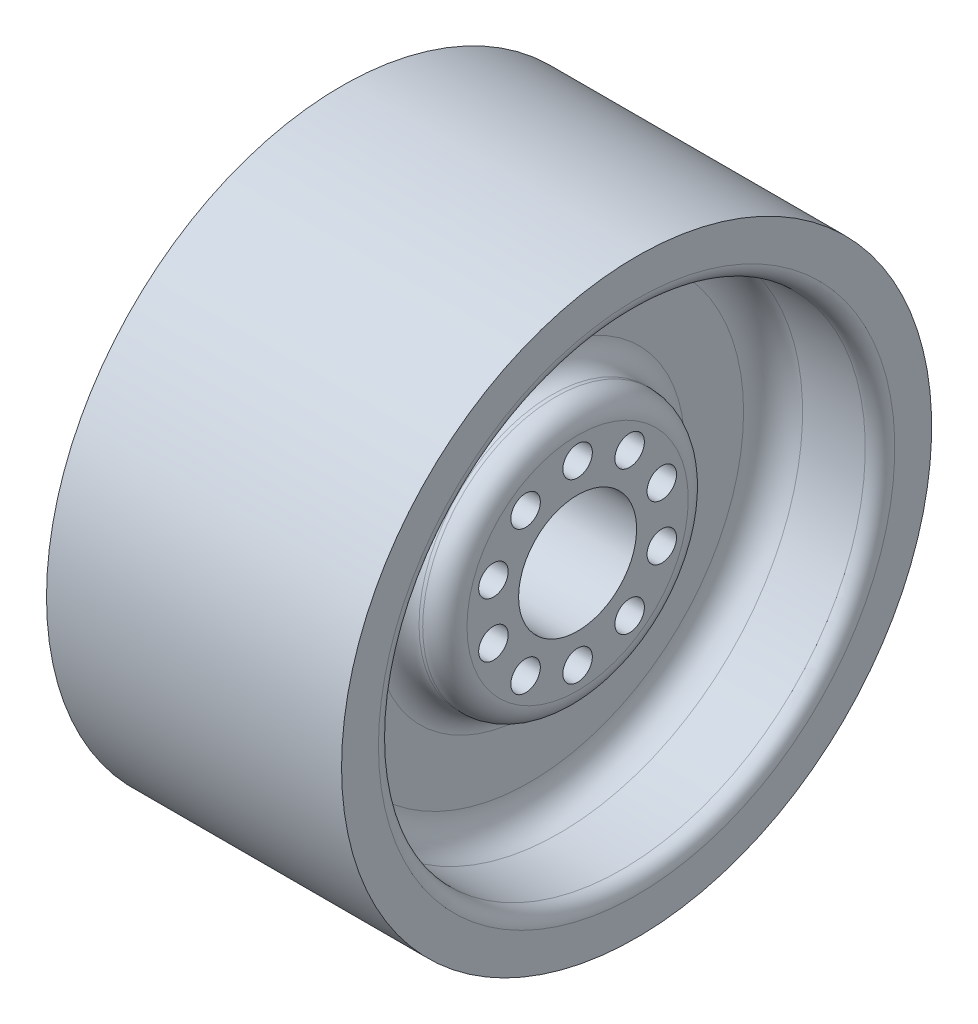
SolidWorks part; units mm, degrees
material "1023 Carbon Steel Sheet (SS)"
ref_plane "Front Plane" through (0, 0, 0) normal (0, 0, 1) x (1, 0, 0)
ref_plane "Top Plane" through (0, 0, 0) normal (0, 1, 0) x (1, 0, 0)
ref_plane "Right Plane" through (0, 0, 0) normal (1, 0, 0) x (0, 0, -1)
sketch "Sketch2" plane through (0, 0, 0) normal (0, 0, 1) x (1, 0, 0)
  line L0 (40, 0) -> (160, 0)
  line L1 (200, 175.001) -> (200, 200.001)
  line L3 (200, 200.001) -> (0, 200.001)
  line L5 (0, 200.001) -> (0, 175.001)
  line L6 (10, 165.001) -> (52.5, 165.001)
  line L7 (72.5, 145.001) -> (72.5, 105)
  line L8 (57.5, 90) -> (55, 90)
  line L9 (40, 75) -> (40, 0)
  line L10 (100, 200.001) -> (100, 36.9891) construction
  line L11 (160, 75) -> (160, 0)
  line L12 (142.5, 90) -> (145, 90)
  line L13 (127.5, 145.001) -> (127.5, 105)
  line L14 (147.5, 165.001) -> (190, 165.001)
  arc A5 (72.5, 105) -> (57.5, 90) centre (57.5, 105) cw
  arc A6 (55, 90) -> (40, 75) centre (55, 75) ccw
  arc A7 (0, 175.001) -> (10, 165.001) centre (10, 175.001) ccw
  arc A8 (72.5, 145.001) -> (52.5, 165.001) centre (52.5, 145.001) ccw
  arc A9 (145, 90) -> (160, 75) centre (145, 75) cw
  arc A10 (127.5, 105) -> (142.5, 90) centre (142.5, 105) ccw
  arc A11 (127.5, 145.001) -> (147.5, 165.001) centre (147.5, 145.001) cw
  arc A12 (200, 175.001) -> (190, 165.001) centre (190, 175.001) cw
  point P10 (100, 200.001)
  point P17 (40, 90)
  dimension "D1" = 10
  dimension "D2" = 200
  dimension "D3" = 35
  dimension "D4" = 90
  dimension "D7" = 15
  dimension "D9" = 20
  dimension "D6" = 60
  dimension "D5" = 27.5
  dimension "D8" = 200.001
revolve "Revolve1" add sketch "Sketch2" angle 360 about L0
sketch "Sketch4" plane through (40, 0, 0) normal (-1, 0, 0) x (0, 0, 1)
  circle A0 centre (0, 0) radius 40
  circle A1 centre (0, 60) radius 10
  circle A2 centre (0, 0) radius 60 construction
  circle A3 centre (35.2671, 48.541) radius 10
  circle A4 centre (57.0634, 18.541) radius 10
  circle A5 centre (57.0634, -18.541) radius 10
  circle A6 centre (35.2671, -48.541) radius 10
  circle A7 centre (0, -60) radius 10
  circle A8 centre (-35.2671, -48.541) radius 10
  circle A9 centre (-57.0634, -18.541) radius 10
  circle A10 centre (-57.0634, 18.541) radius 10
  circle A11 centre (-35.2671, 48.541) radius 10
  point P26 (0, 0)
  dimension "D1" = 80
  dimension "D2" = 20
  dimension "D3" = 120
  dimension "D4" = 10
extrude "Cut-Extrude2" cut sketch "Sketch4" against normal through all
